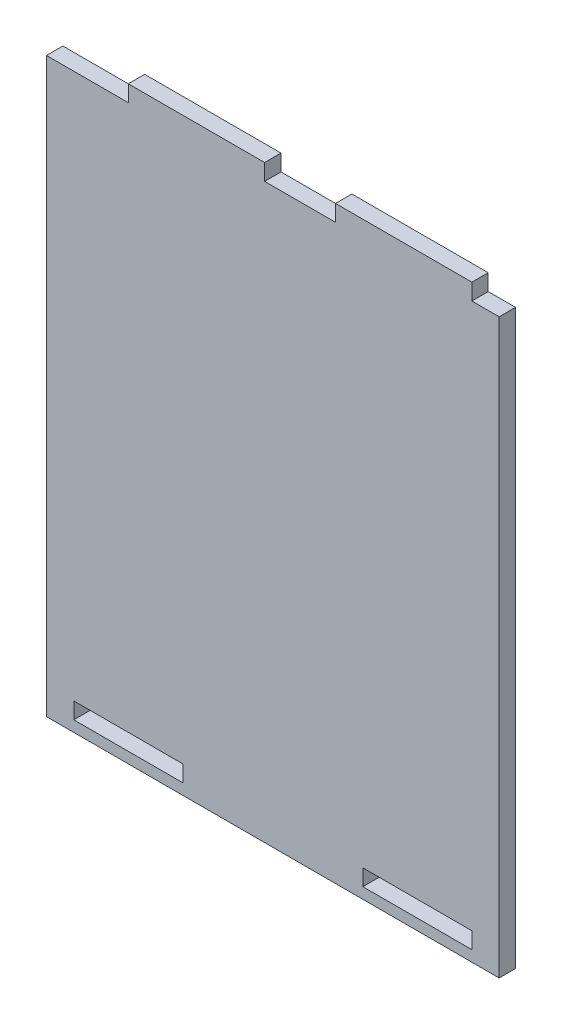
SolidWorks part; units mm, degrees
material "Carvalho"
ref_plane "Plano frontal" through (0, 0, 0) normal (0, 0, 1) x (1, 0, 0)
ref_plane "Plano superior" through (0, 0, 0) normal (0, 1, 0) x (1, 0, 0)
ref_plane "Plano direito" through (0, 0, 0) normal (1, 0, 0) x (0, 0, -1)
sketch "Esboço1" plane through (0, 0, 0) normal (0, 0, 1) x (1, 0, 0)
  line L0 (-26.5141, 42.5155) -> (-13.5141, 42.5155)
  line L1 (-66.5141, -62.4845) -> (16.4859, -62.4845)
  line L2 (-66.5141, -62.4845) -> (-66.5141, 42.5155)
  line L3 (-66.5141, 42.5155) -> (-51.5141, 42.5155)
  line L4 (16.4859, -62.4845) -> (16.4859, 42.5155)
  line L5 (11.4859, 42.5155) -> (16.4859, 42.5155)
  line L6 (-51.5141, 42.5155) -> (-51.5141, 45.5155)
  line L7 (-51.5141, 45.5155) -> (-26.5141, 45.5155)
  line L8 (-26.5141, 42.5155) -> (-26.5141, 45.5155)
  line L10 (-13.5141, 42.5155) -> (-13.5141, 45.5155)
  line L11 (-13.5141, 45.5155) -> (11.4859, 45.5155)
  line L12 (11.4859, 42.5155) -> (11.4859, 45.5155)
  dimension "D1" = 105
  dimension "D2" = 15
  dimension "D3" = 25
  dimension "D4" = 25
  dimension "D5" = 13
  dimension "D6" = 5
  dimension "D7" = 3
  dimension "D8" = 3
extrude "Ressalto-extrusão1" add sketch "Esboço1" along normal blind 3
sketch "Esboço2" plane through (0, 0, 0) normal (0, 0, -1) x (-1, 0, 0)
  line L0 (66.5141, -62.4845) -> (-16.4859, -62.4845) construction
  line L1 (61.5141, -57.4845) -> (41.5141, -57.4845)
  line L2 (61.5141, -57.4845) -> (61.5141, -60.4845)
  line L3 (61.5141, -60.4845) -> (41.5141, -60.4845)
  line L4 (41.5141, -57.4845) -> (41.5141, -60.4845)
  line L5 (8.5141, -57.4845) -> (-11.4859, -57.4845)
  line L6 (8.5141, -57.4845) -> (8.5141, -60.4845)
  line L7 (8.5141, -60.4845) -> (-11.4859, -60.4845)
  line L8 (-11.4859, -57.4845) -> (-11.4859, -60.4845)
  line L9 (66.5141, 42.5155) -> (66.5141, -62.4845) construction
  line L10 (-16.4859, -62.4845) -> (-16.4859, 42.5155) construction
  dimension "D1" = 3
  dimension "D2" = 3
  dimension "D3" = 2
  dimension "D4" = 2
  dimension "D5" = 20
  dimension "D6" = 5
  dimension "D7" = 5
  dimension "D8" = 20
extrude "Corte-extrusão1" cut sketch "Esboço2" against normal through all
